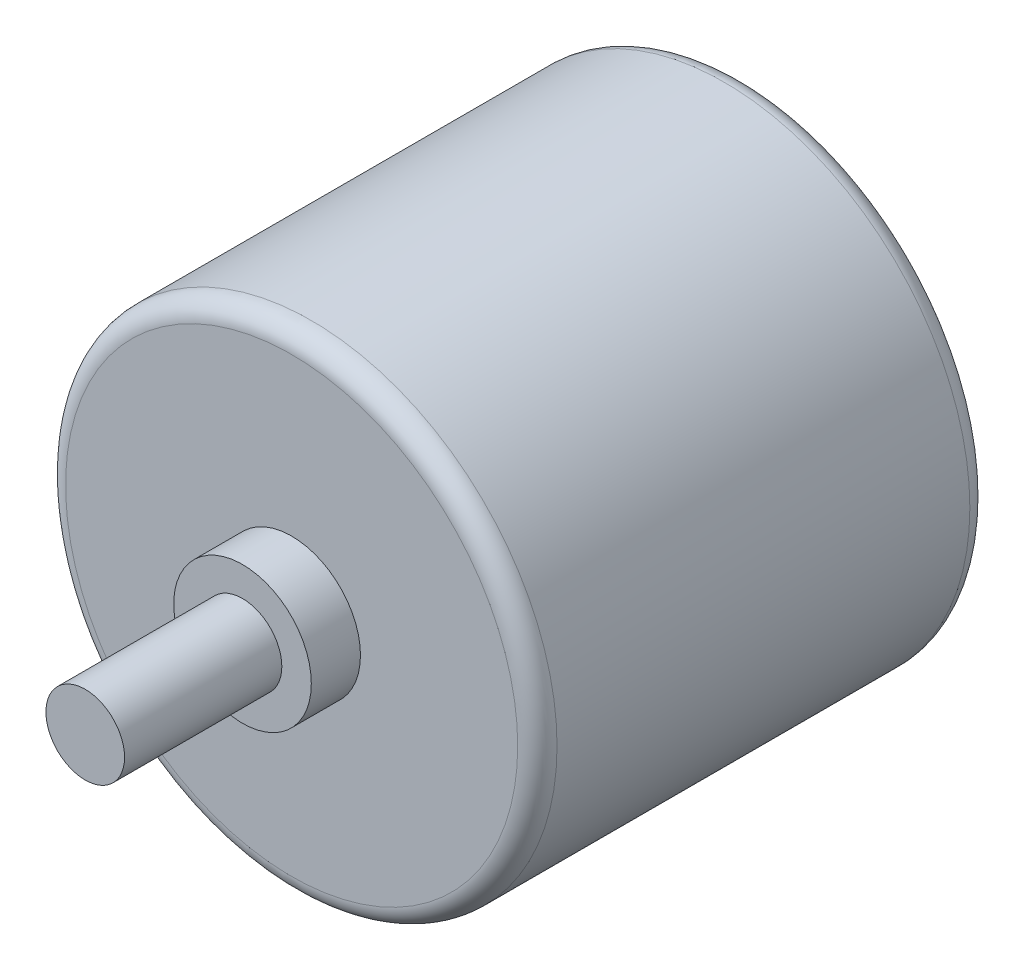
SolidWorks part; units mm, degrees
material "201.0-T43 Molde de fundição com isolamento (SS)"
ref_plane "Plano frontal" through (0, 0, 0) normal (0, 0, 1) x (1, 0, 0)
ref_plane "Plano superior" through (0, 0, 0) normal (0, 1, 0) x (1, 0, 0)
ref_plane "Plano direito" through (0, 0, 0) normal (1, 0, 0) x (0, 0, -1)
sketch "Esboço1" plane through (0, 0, 0) normal (0, 0, 1) x (1, 0, 0)
  circle A0 centre (0, 0) radius 12.5
  dimension "D1" = 25
extrude "Ressalto-extrusão1" add sketch "Esboço1" along normal blind 23
sketch "Esboço2" plane through (0, 0, 23) normal (0, 0, 1) x (1, 0, 0)
  circle A0 centre (0, 0) radius 3.5
  dimension "D1" = 7
extrude "Ressalto-extrusão2" add sketch "Esboço2" along normal blind 2.5
sketch "Esboço3" plane through (0, 0, 25.5) normal (0, 0, 1) x (1, 0, 0)
  circle A0 centre (0, 0) radius 2
  dimension "D1" = 4
fillet "Filete1" radius 1 2 edges at (12.5, 0, 23) (12.5, 0, 0)
extrude "Ressalto-extrusão3" add sketch "Esboço3" along normal blind 8
